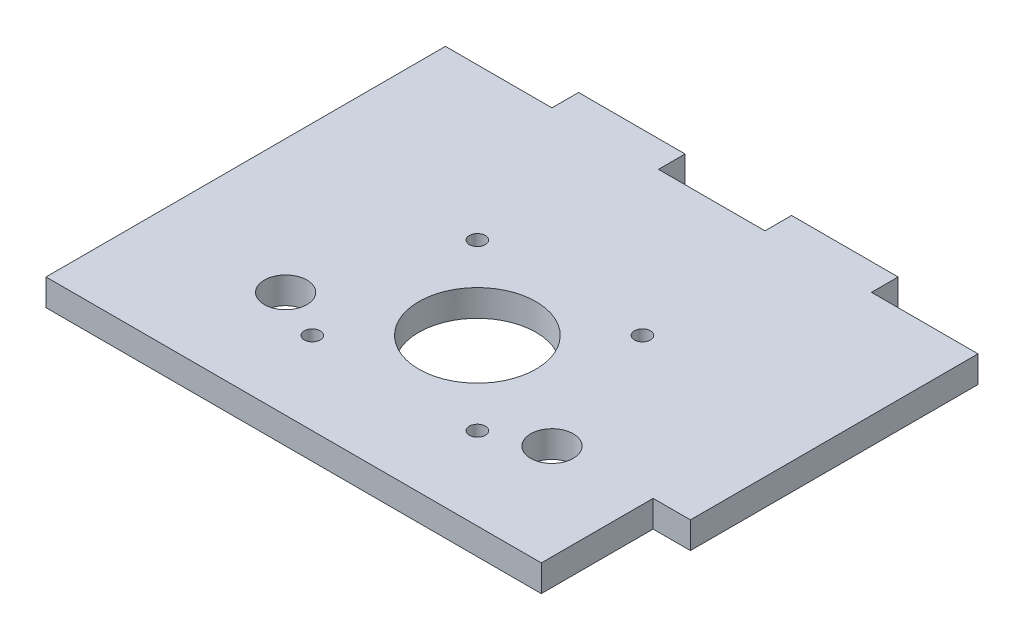
SolidWorks part; units mm, degrees
material "Acrylic (Medium-high impact)"
ref_plane "Front Plane" through (0, 0, 0) normal (0, 0, 1) x (1, 0, 0)
ref_plane "Top Plane" through (0, 0, 0) normal (0, 1, 0) x (1, 0, 0)
ref_plane "Right Plane" through (0, 0, 0) normal (1, 0, 0) x (0, 0, -1)
sketch "Sketch1" plane through (0, 0, 0) normal (0, 1, 0) x (1, 0, 0)
  line L0 (-1000, 0) -> (49000, 0) construction
  line L5 (0, -1000) -> (0, 49000) construction
  line L6 (-50, 44) -> (-30, 44)
  line L7 (-50, -31) -> (50, -31)
  line L8 (-50, -31) -> (-50, 44)
  line L9 (-30, 49) -> (-10, 49)
  line L10 (50, -31) -> (50, 44)
  line L11 (-30, 49) -> (-30, 44)
  line L12 (-10, 49) -> (-10, 44)
  line L13 (10, 49) -> (10, 44)
  line L14 (30, 49) -> (30, 44)
  line L16 (30, 44) -> (50, 44)
  line L17 (10, 49) -> (30, 49)
  line L18 (-10, 44) -> (10, 44)
  circle A10 centre (0, 0) radius 4
  circle A11 centre (15.5, 15.5) radius 1.5
  circle A12 centre (-15.5, 15.5) radius 1.5
  circle A13 centre (-15.5, -15.5) radius 1.5
  circle A14 centre (15.5, -15.5) radius 1.5
  circle A16 centre (-25, -11) radius 4
  circle A17 centre (25, -11) radius 4
  point P6 (0, 44)
  dimension "D3" = 8
  dimension "D4" = 15.5
  dimension "D6" = 3
  dimension "D12" = 25
  dimension "D13" = 31
  dimension "D2" = 100
  dimension "D5" = 15.5
  dimension "D7" = 5
  dimension "D9" = 4
  dimension "D8" = 20
  dimension "D10" = 20
  dimension "D11" = 80
  dimension "D14" = 20
extrude "Boss-Extrude1" add sketch "Sketch1" along normal blind 5
sketch "Sketch2" plane through (0, 5, 0) normal (0, 1, 0) x (1, 0, 0)
  circle A0 centre (0, 0) radius 11
  dimension "D1" = 22
extrude "Cut-Extrude1" cut sketch "Sketch2" against normal up to next
sketch "Sketch3" plane through (50, 0, 0) normal (1, 0, 0) x (0, 0, -1)
  line L0 (-31, 5) -> (44, 5) construction
  line L1 (-31, 0) -> (-10, 0)
  line L2 (-31, 0) -> (-31, 5)
  line L3 (-31, 5) -> (-10, 5)
  line L4 (-10, 0) -> (-10, 5)
  dimension "D1" = 21
extrude "Cut-Extrude2" cut sketch "Sketch3" against normal blind 7
